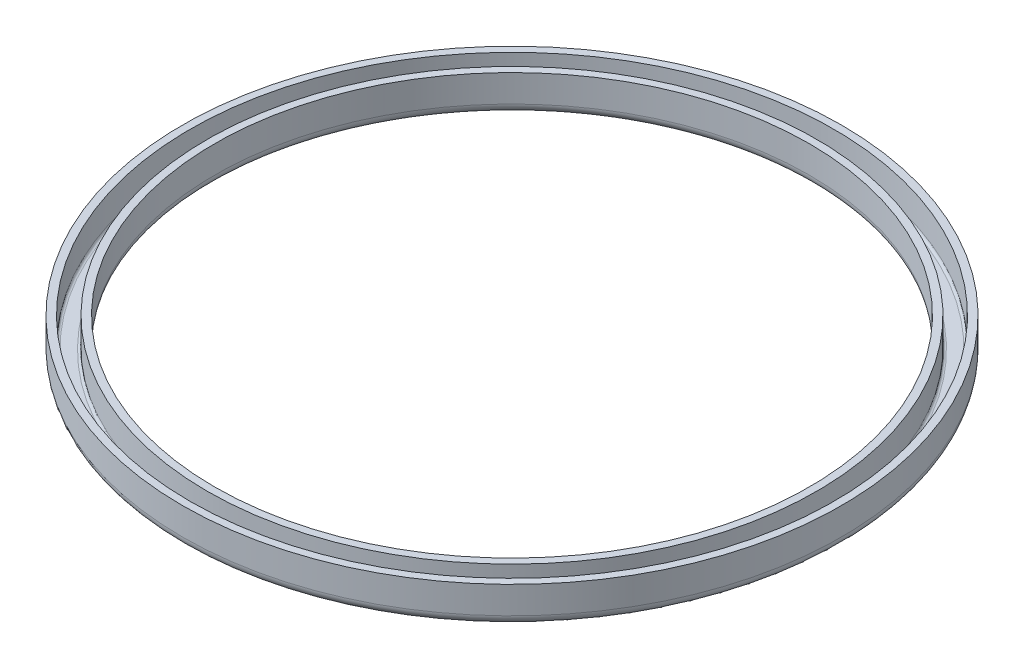
SolidWorks part; units mm, degrees
ref_plane "Front Plane" through (0, 0, 0) normal (0, 0, 1) x (1, 0, 0)
ref_plane "Top Plane" through (0, 0, 0) normal (0, 1, 0) x (1, 0, 0)
ref_plane "Right Plane" through (0, 0, 0) normal (1, 0, 0) x (0, 0, -1)
sketch "Sketch1" plane through (0, 0, 0) normal (0, 0, 1) x (1, 0, 0)
  line L0 (0, 25.195) -> (0, -41.3786) construction
  line L1 (0, -55) -> (0, 55) construction
  line L2 (-6.65, 0.75) -> (-6.65, 0.2)
  line L3 (55, 0) -> (-55, 0) construction
  line L4 (-6.45, 0) -> (-6.2, 0)
  line L5 (-6, 0.2) -> (-6, 0.75)
  arc A0 (-6.65, 0.2) -> (-6.45, 0) centre (-6.45, 0.2) ccw
  arc A1 (-6, 0.2) -> (-6.2, 0) centre (-6.2, 0.2) cw
  point P13 (-6.65, 0)
  point P16 (-6, 0)
  dimension "D1" = 0.2
  dimension "D2" = 0.65
  dimension "D3" = 0.75
  dimension "D4" = 13.3
revolve "Revolve-Thin1" add sketch "Sketch1" angle 360 about L0 wall 0.15
